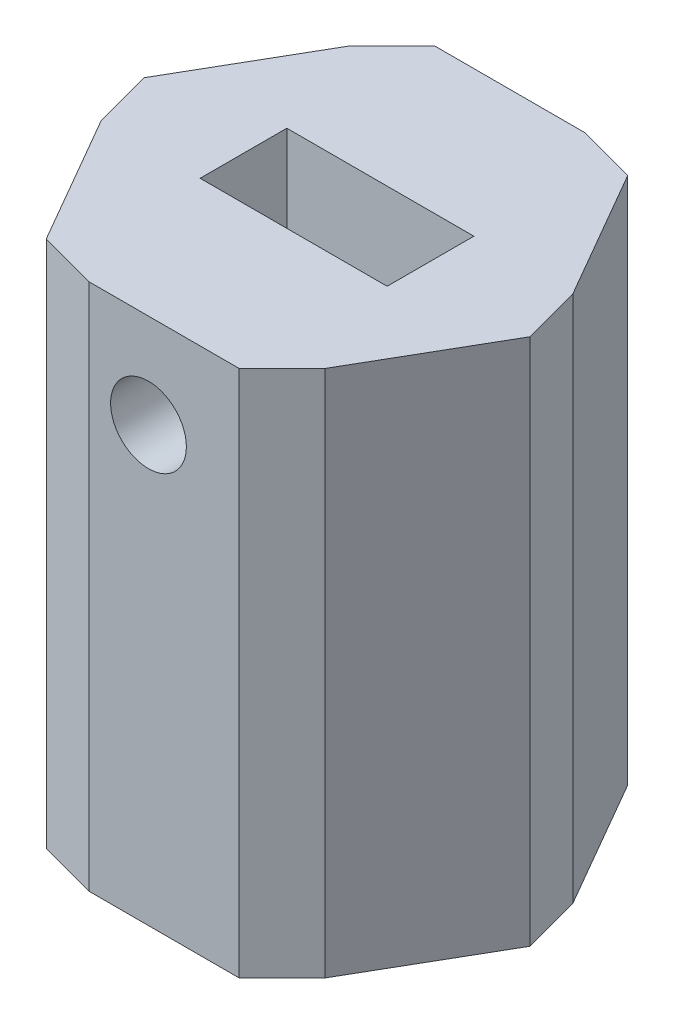
SolidWorks part; units mm, degrees
ref_plane "Front Plane" through (0, 0, 0) normal (0, 0, 1) x (1, 0, 0)
ref_plane "Top Plane" through (0, 0, 0) normal (0, 1, 0) x (1, 0, 0)
ref_plane "Right Plane" through (0, 0, 0) normal (1, 0, 0) x (0, 0, -1)
sketch "Sketch1" plane through (0, 0, 0) normal (0, 1, 0) x (1, 0, 0)
  line L1 (-14.6647, 0) -> (-7.3323, -12.7)
  line L2 (-7.3323, -12.7) -> (7.3323, -12.7)
  line L3 (7.3323, -12.7) -> (14.6647, 0)
  line L4 (14.6647, 0) -> (7.3323, 12.7)
  line L5 (7.3323, 12.7) -> (-7.3323, 12.7)
  line L6 (-7.3323, 12.7) -> (-14.6647, 0)
  circle A0 centre (0, 0) radius 12.7 construction
  dimension "D1" = 25.4
extrude "Boss-Extrude1" add sketch "Sketch1" along normal blind 35.56
sketch "Sketch2" plane through (0, 35.56, 0) normal (0, 1, 0) x (1, 0, 0)
  line L1 (6.2997, 2.921) -> (-6.2997, 2.921)
  line L2 (6.2997, 2.921) -> (6.2997, -2.921)
  line L3 (6.2997, -2.921) -> (-6.2997, -2.921)
  line L4 (-6.2997, 2.921) -> (-6.2997, -2.921)
  line L5 (6.2997, 2.921) -> (-6.2997, -2.921) construction
  line L6 (6.2997, -2.921) -> (-6.2997, 2.921) construction
  point P0 (0, 0)
  dimension "D1" = 5.842
  dimension "D2" = 12.5995
extrude "Cut-Extrude1" cut sketch "Sketch2" against normal blind 12.7
sketch "Sketch3" plane through (0, 0, 0) normal (0, -1, 0) x (1, 0, 0)
  line L1 (0, 6.4658) -> (-6.4658, 0)
  line L2 (0, 6.4658) -> (6.4658, 0)
  line L3 (6.4658, 0) -> (0, -6.4658)
  line L4 (-6.4658, 0) -> (0, -6.4658)
  line L5 (0, 6.4658) -> (0, -6.4658) construction
  line L6 (6.4658, 0) -> (-6.4658, 0) construction
  point P0 (0, 0)
  dimension "D1" = 9.144
extrude "Cut-Extrude2" cut sketch "Sketch3" against normal blind 12.7
hole_wizard "1/4-20 Tapped Hole1" positions "Sketch4" profile "Sketch6" tap size "1/4-20" standard "ANSI Inch"
sketch "Sketch4" plane through (0, 0, 12.7) normal (0, 0, 1) x (1, 0, 0)
  line L0 (-7.3323, 35.56) -> (7.3323, 35.56) construction
  point P0 (0, 29.21)
  dimension "D1" = 6.35
sketch "Sketch6" plane through (0, 29.21, 12.7) normal (1, 0, 0) x (0, -1, 0)
  line L0 (0, 0) -> (0, 15.62)
  line L1 (0, 15.62) -> (2.5527, 14.0862)
  line L2 (2.5527, 14.0862) -> (2.5527, 0)
  line L5 (2.5527, 0) -> (0, 0)
  line L10 (0, 15.62) -> (-2.5527, 14.0862) construction
  line L11 (0, -6.35) -> (0, 107.95) construction
  dimension "Tap Drill Dia." = 5.1054
  dimension "Tap Drill Depth" = 15.62
  dimension "Drill Angle" = 118
cosmetic thread "Hole Thread2" parameters "D1"=12.7, "D2"=6.35
chamfer "Chamfer1" distance 1.2192 angle 45 10 edges at (0, 6.35, -6.4658) (6.4658, 6.35, 0) (-6.4658, 6.35, 0) (0, 6.35, 6.4658) (-7.3323, 17.78, -12.7) (7.3323, 17.78, -12.7) (14.6647, 17.78, 0) (7.3323, 17.78, 12.7) (-7.3323, 17.78, 12.7) (-14.6647, 17.78, 0)
sketch "Sketch7" plane through (0, 0, 0) normal (0, 1, 0) x (1, 0, 0)
  circle A0 centre (0, 0) radius 6.35 construction
  dimension "D1" = 12.7
